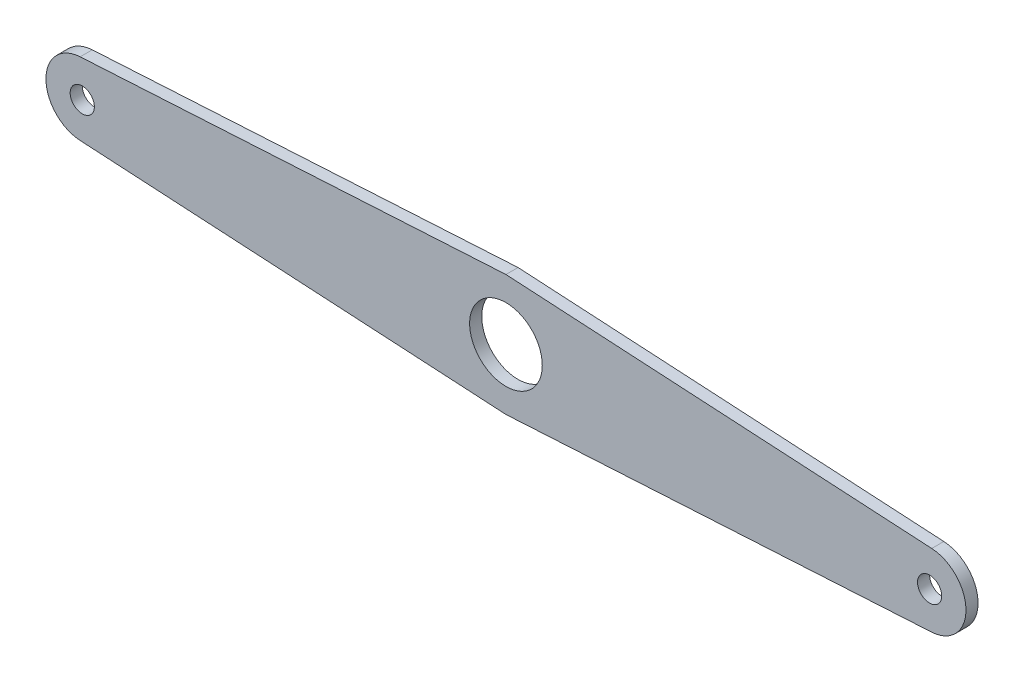
SolidWorks part; units mm, degrees
material "AISI 1020"
ref_plane "Front Plane" through (0, 0, 0) normal (0, 0, 1) x (1, 0, 0)
ref_plane "Top Plane" through (0, 0, 0) normal (0, 1, 0) x (1, 0, 0)
ref_plane "Right Plane" through (0, 0, 0) normal (1, 0, 0) x (0, 0, -1)
sketch "Sketch1" plane through (0, 0, 0) normal (0, 0, 1) x (1, 0, 0)
  line L0 (-175, 0) -> (0, 0) construction
  line L1 (0, 0) -> (175, 0) construction
  line L2 (0, 0) -> (0, 100) construction
  line L3 (-175.8571, 14.9755) -> (0, 25.0409)
  line L4 (-175.8571, -14.9755) -> (0, -25.0409)
  line L5 (175.8571, -14.9755) -> (0, -25.0409)
  line L6 (175.8571, 14.9755) -> (0, 25.0409)
  circle A0 centre (-175, 0) radius 5
  circle A1 centre (175, 0) radius 5
  circle A2 centre (0, 0) radius 15
  circle A3 centre (-175, 0) radius 15 construction
  circle A4 centre (175, 0) radius 15 construction
  circle A5 centre (0, 0) radius 25 construction
  arc A6 (-175.8571, 14.9755) -> (-175, -15) centre (-175, 0) ccw
  arc A7 (175.8571, 14.9755) -> (175.8571, -14.9755) centre (175, 0) cw
  dimension "D2" = 10
  dimension "D3" = 10
  dimension "D4" = 30
  dimension "D1" = 350
  dimension "D6" = 100
  dimension "D5" = 10
extrude "Boss-Extrude1" add sketch "Sketch1" along normal blind 5
